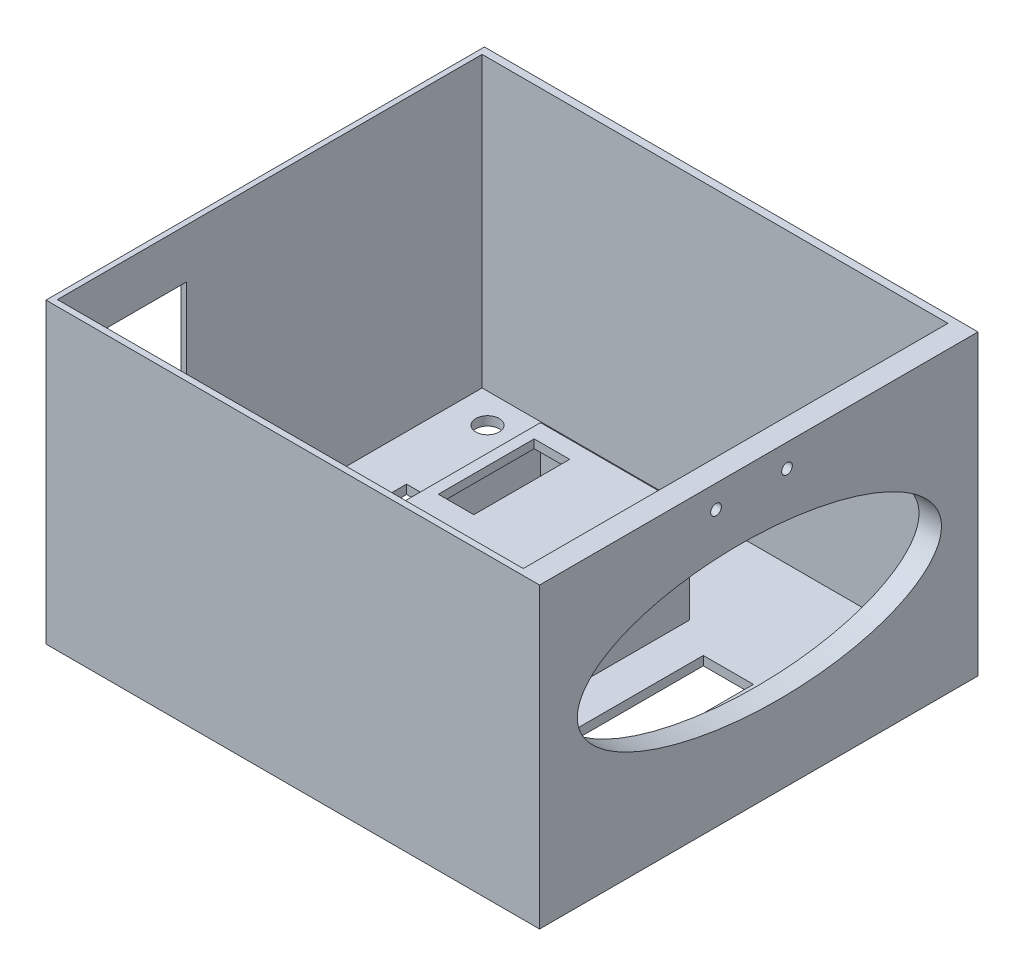
SolidWorks part; units mm, degrees
ref_plane "Front Plane" through (0, 0, 0) normal (0, 0, 1) x (1, 0, 0)
ref_plane "Top Plane" through (0, 0, 0) normal (0, 1, 0) x (1, 0, 0)
ref_plane "Right Plane" through (0, 0, 0) normal (1, 0, 0) x (0, 0, -1)
sketch "Sketch1" plane through (0, 0, 0) normal (0, 1, 0) x (1, 0, 0)
  line L1 (-72.9004, 101.3487) -> (91.0996, 101.3487)
  line L2 (-72.9004, 101.3487) -> (-72.9004, -44.3313)
  line L3 (-72.9004, -44.3313) -> (91.0996, -44.3313)
  line L4 (91.0996, 101.3487) -> (91.0996, -44.3313)
extrude "Boss-Extrude1" add sketch "Sketch1" along normal blind 3
sketch "Sketch2" plane through (0, 3, 0) normal (0, 1, 0) x (1, 0, 0)
  line L1 (-72.9004, 101.3487) -> (91.0996, 101.3487)
  line L2 (-72.9004, 101.3487) -> (-72.9004, -44.3313)
  line L3 (-72.9004, -44.3313) -> (91.0996, -44.3313)
  line L4 (91.0996, 101.3487) -> (91.0996, -44.3313)
  line L5 (-71.1533, 98.8274) -> (83.6411, 98.8274)
  line L6 (-71.1533, 98.8274) -> (-71.1533, -42.2955)
  line L7 (-71.1533, -42.2955) -> (83.6411, -42.2955)
  line L8 (83.6411, 98.8274) -> (83.6411, -42.2955)
  point P10 (83.6411, 98.8274)
extrude "Boss-Extrude2" add sketch "Sketch2" along normal blind 96
sketch "Sketch4" plane through (91.0996, 0, 0) normal (1, 0, 0) x (0, 0, -1)
  ellipse E0 centre (28.7147, 51.8583) end of major axis (89.1968, 48.5753) minor radius 25.3855
  point P0 (-32.2054, 51.8583)
  point P5 (155.077, 54.4142)
  point P11 (79.5047, 76.1899)
  point P12 (59.1645, 54.4142)
  point P13 (-29.6059, 54.4142)
  point P14 (83.4628, 54.4142)
  point P15 (-12.137, 54.4142)
  point P16 (30.5158, 49.3024)
extrude "Cut-Extrude1" cut sketch "Sketch4" against normal blind 20
sketch "Sketch6" plane through (-72.9004, 0, 0) normal (-1, 0, 0) x (0, 0, 1)
  line L1 (-0.5419, 6.9674) -> (39.2483, 6.9674)
  line L2 (-0.5419, 6.9674) -> (-0.5419, 82.619)
  line L3 (-0.5419, 82.619) -> (39.2483, 82.619)
  line L4 (39.2483, 6.9674) -> (39.2483, 82.619)
extrude "Cut-Extrude3" cut sketch "Sketch6" against normal blind 20
sketch "Sketch8" plane through (0, 3, 0) normal (0, 1, 0) x (1, 0, 0)
  line L1 (-19.4695, -25.2998) -> (30.0997, -25.2998)
  line L2 (-19.4695, -25.2998) -> (-19.4695, 66.5493)
  line L3 (-19.4695, 66.5493) -> (30.0997, 66.5493)
  line L4 (30.0997, -25.2998) -> (30.0997, 66.5493)
extrude "Boss-Extrude3" add sketch "Sketch8" along normal blind 32
sketch "Sketch7" plane through (0, 0, 0) normal (0, -1, 0) x (1, 0, 0)
  line L1 (-17.266, 22.9636) -> (27.734, 22.9636)
  line L2 (-17.266, 22.9636) -> (-17.266, -64.3464)
  line L3 (-17.266, -64.3464) -> (27.734, -64.3464)
  line L4 (27.734, 22.9636) -> (27.734, -64.3464)
  point P4 (5.234, 22.9636)
extrude "Cut-Extrude4" cut sketch "Sketch7" against normal blind 32.17
sketch "Sketch9" plane through (0, 32.17, 0) normal (0, -1, 0) x (1, 0, 0)
  line L1 (-4.0607, -60.8382) -> (-15.8579, -60.8382)
  line L2 (-4.0607, -60.8382) -> (-4.0607, -28.9718)
  line L3 (-4.0607, -28.9718) -> (-15.8579, -28.9718)
  line L4 (-15.8579, -60.8382) -> (-15.8579, -28.9718)
extrude "Cut-Extrude5" cut sketch "Sketch9" against normal blind 40
sketch "Sketch10" plane through (0, 32.17, 0) normal (0, -1, 0) x (1, 0, 0)
  line L1 (25.8116, -11.3729) -> (14.1238, -11.3729)
  line L2 (25.8116, -11.3729) -> (25.8116, 20.0569)
  line L3 (25.8116, 20.0569) -> (14.1238, 20.0569)
  line L4 (14.1238, -11.3729) -> (14.1238, 20.0569)
sketch "Sketch11" plane through (0, 0, 0) normal (0, -1, 0) x (1, 0, 0)
  line L1 (59.2163, -58.6112) -> (42.5661, -58.6112)
  line L2 (59.2163, -58.6112) -> (59.2163, 15.7034)
  line L3 (59.2163, 15.7034) -> (42.5661, 15.7034)
  line L4 (42.5661, -58.6112) -> (42.5661, 15.7034)
  line L5 (-31.5288, -58.6112) -> (-56.0347, -58.6112)
  line L6 (-31.5288, -58.6112) -> (-31.5288, 15.7034)
  line L7 (-31.5288, 15.7034) -> (-56.0347, 15.7034)
  line L8 (-56.0347, -58.6112) -> (-56.0347, 15.7034)
extrude "Cut-Extrude7" cut sketch "Sketch11" against normal blind 40
sketch "Sketch12" plane through (91.0996, 0, 0) normal (1, 0, 0) x (0, 0, -1)
  line L0 (73.1094, 91.3917) -> (-25.807, 91.3917) construction
  circle A0 centre (37.8774, 91.3917) radius 1.77
  circle A1 centre (14.3001, 91.3917) radius 1.774
  point P6 (0, 0)
extrude "Cut-Extrude8" cut sketch "Sketch12" against normal blind 40
sketch "Sketch13" plane through (0, 0, 0) normal (0, -1, 0) x (1, 0, 0)
  circle A0 centre (-59.5348, -89.004) radius 3.8935
extrude "Cut-Extrude9" cut sketch "Sketch13" against normal blind 40
